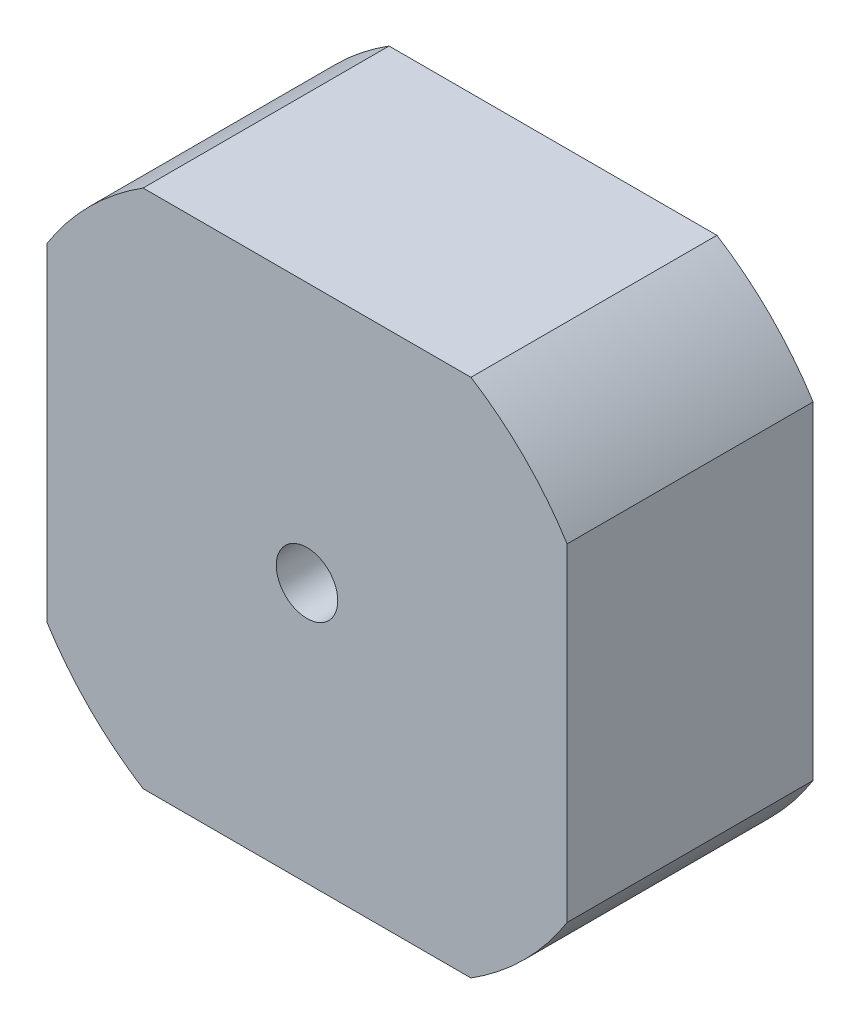
SolidWorks part; units mm, degrees
ref_plane "Alzado" through (0, 0, 0) normal (0, 0, 1) x (1, 0, 0)
ref_plane "Planta" through (0, 0, 0) normal (0, 1, 0) x (1, 0, 0)
ref_plane "Vista lateral" through (0, 0, 0) normal (1, 0, 0) x (0, 0, -1)
sketch "Croquis1" plane through (0, 0, 0) normal (0, 0, 1) x (1, 0, 0)
  line L1 (-13.3296, -21.15) -> (13.3296, -21.15)
  line L2 (-21.15, -13.3296) -> (-21.15, 13.3296)
  line L3 (-13.3296, 21.15) -> (13.3296, 21.15)
  line L4 (21.15, -13.3296) -> (21.15, 13.3296)
  line L5 (-17.6777, -17.6777) -> (17.6777, 17.6777) construction
  line L6 (-17.6777, 17.6777) -> (17.6777, -17.6777) construction
  arc A0 (-13.3296, 21.15) -> (-21.15, 13.3296) centre (0, 0) ccw
  arc A1 (-21.15, -13.3296) -> (-13.3296, -21.15) centre (0, 0) ccw
  arc A2 (13.3296, -21.15) -> (21.15, -13.3296) centre (0, 0) ccw
  arc A3 (21.15, 13.3296) -> (13.3296, 21.15) centre (0, 0) ccw
  point P0 (0, 0)
  dimension "D2" = 25
  dimension "D1" = 26.6591
extrude "Saliente-Extruir1" add sketch "Croquis1" along normal blind 20
sketch "Croquis2" plane through (0, 0, 20) normal (0, 0, 1) x (1, 0, 0)
  circle A0 centre (0, 0) radius 2.5
  dimension "D1" = 5
extrude "Cortar-Extruir1" cut sketch "Croquis2" against normal through all
